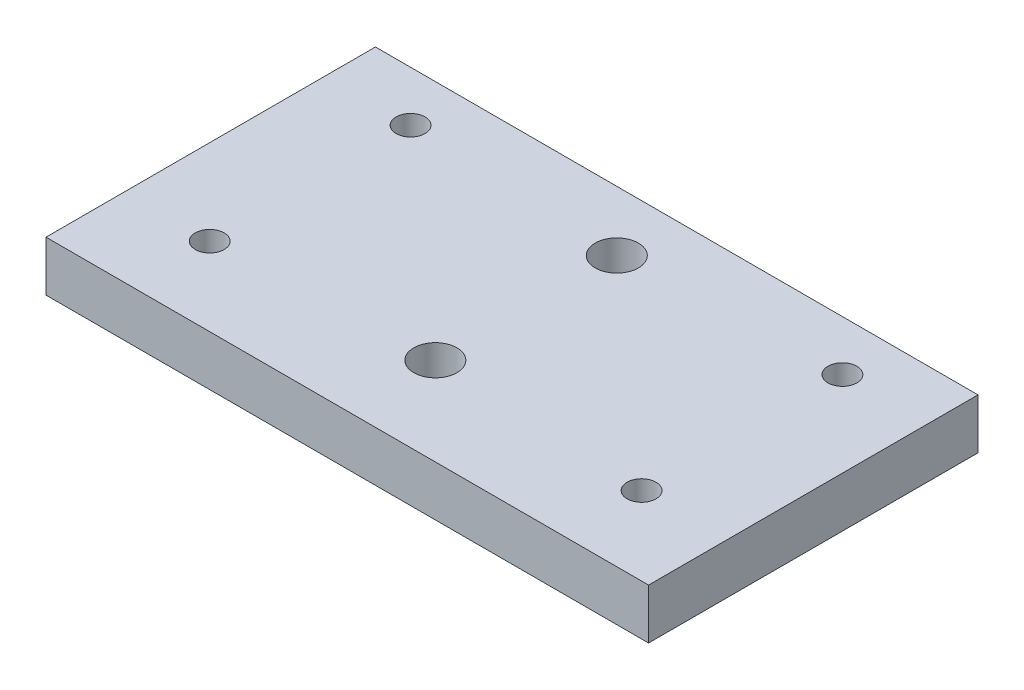
SolidWorks part; units mm, degrees
ref_plane "Front Plane" through (0, 0, 0) normal (0, 0, 1) x (1, 0, 0)
ref_plane "Top Plane" through (0, 0, 0) normal (0, 1, 0) x (1, 0, 0)
ref_plane "Right Plane" through (0, 0, 0) normal (1, 0, 0) x (0, 0, -1)
sketch "Sketch1" plane through (0, 0, 0) normal (0, 1, 0) x (1, 0, 0)
  line L0 (0, 76.2) -> (0, 57.15) construction
  line L1 (-38.1, 76.2) -> (38.1, 76.2)
  line L2 (-38.1, 76.2) -> (-38.1, -76.2)
  line L3 (-38.1, -76.2) -> (38.1, -76.2)
  line L4 (38.1, 76.2) -> (38.1, -76.2)
  line L5 (-38.1, 76.2) -> (38.1, -76.2) construction
  line L6 (-38.1, -76.2) -> (38.1, 76.2) construction
  line L7 (0, 57.15) -> (27.305, 57.15) construction
  line L8 (27.305, 57.15) -> (27.305, 44.45) construction
  circle A0 centre (0, 57.15) radius 2.7305 construction
  circle A1 centre (0, 19.05) radius 2.7305
  circle A2 centre (0, -19.05) radius 2.7305
  circle A3 centre (0, -57.15) radius 2.7305
  circle A4 centre (27.305, 44.45) radius 1.8288
  circle A5 centre (27.305, 6.35) radius 1.8288
  circle A6 centre (27.305, -31.75) radius 1.8288
  circle A7 centre (-27.305, 6.35) radius 1.8288
  circle A8 centre (-27.305, -31.75) radius 1.8288
  circle A9 centre (-27.305, 44.45) radius 1.8288
  circle A10 centre (0, 45.678) radius 2.7305
  circle A11 centre (27.305, 69.85) radius 1.8288
  circle A12 centre (-27.305, 69.85) radius 1.8288
  circle A13 centre (0, 68.622) radius 2.7305
  point P0 (0, 0)
  dimension "D4" = 5.461
  dimension "D10" = 3.6576
  dimension "D11" = 5.461
  dimension "D1" = 76.2
  dimension "D2" = 152.4
  dimension "D3" = 19.05
  dimension "D6" = 27.305
  dimension "D7" = 12.7
  dimension "D5" = 4
  dimension "D8" = 3
  dimension "D9" = 2
extrude "Boss-Extrude1" add sketch "Sketch1" against normal blind 6.35
sketch "Sketch2" plane through (0, 0, 0) normal (0, 1, 0) x (1, 0, 0)
  line L0 (-38.1, 76.2) -> (-38.1, -76.2) construction
  line L1 (38.1, -76.2) -> (-38.1, -76.2)
  line L2 (38.1, -76.2) -> (38.1, 34.5402)
  line L3 (38.1, 34.5402) -> (-38.1, 34.5402)
  line L4 (-38.1, -76.2) -> (-38.1, 34.5402)
extrude "Cut-Extrude1" cut sketch "Sketch2" against normal through all both and the other way through all
